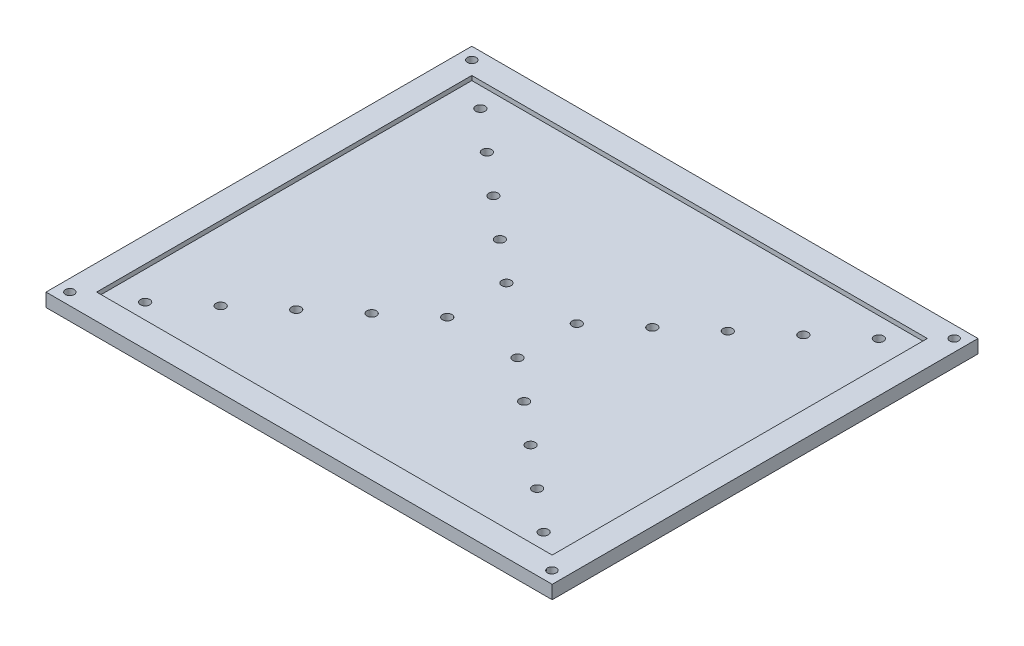
SolidWorks part; units mm, degrees
ref_plane "Front Plane" through (0, 0, 0) normal (0, 0, 1) x (1, 0, 0)
ref_plane "Top Plane" through (0, 0, 0) normal (0, 1, 0) x (1, 0, 0)
ref_plane "Right Plane" through (0, 0, 0) normal (1, 0, 0) x (0, 0, -1)
sketch "Sketch1" plane through (0, 0, 0) normal (0, 1, 0) x (1, 0, 0)
  line L1 (-94.45, 79.45) -> (94.45, 79.45)
  line L2 (-94.45, 79.45) -> (-94.45, -79.45)
  line L3 (-94.45, -79.45) -> (94.45, -79.45)
  line L4 (94.45, 79.45) -> (94.45, -79.45)
  point P4 (0, 79.45)
  point P6 (-94.45, 0)
  dimension "D1" = 158.9
  dimension "D2" = 188.9
extrude "Boss-Extrude1" add sketch "Sketch1" along normal blind 5
sketch "Sketch2" plane through (0, 5, 0) normal (0, 1, 0) x (1, 0, 0)
  line L0 (-94.45, 79.45) -> (-94.45, -79.45) construction
  line L1 (-85, 70) -> (85, 70)
  line L2 (-85, 70) -> (-85, -70)
  line L3 (-85, -70) -> (85, -70)
  line L4 (85, 70) -> (85, -70)
  line L5 (94.45, 79.45) -> (-94.45, 79.45) construction
  point P8 (-85, 0)
  point P10 (0, 70)
  dimension "D1" = 9.45
  dimension "D2" = 9.45
extrude "Cut-Extrude1" cut sketch "Sketch2" against normal blind 1.66
sketch "Sketch3" plane through (0, 5, 0) normal (0, 1, 0) x (1, 0, 0)
  line L0 (-94.45, 79.45) -> (-94.45, -79.45) construction
  line L1 (94.45, 79.45) -> (-94.45, 79.45) construction
  circle A0 centre (-90, 75) radius 1.65
  dimension "D1" = 3.3
  dimension "D2" = 4.45
  dimension "D3" = 4.45
extrude "Cut-Extrude2" cut sketch "Sketch3" against normal blind 5 contours A0
sketch "Sketch6" plane through (0, 5, 0) normal (0, 1, 0) x (1, 0, 0)
  line L0 (-94.45, -79.45) -> (94.45, -79.45) construction
  line L1 (-94.45, 79.45) -> (-94.45, -79.45) construction
  line L2 (94.45, -79.45) -> (94.45, 79.45) construction
  line L3 (94.45, 79.45) -> (-94.45, 79.45) construction
  circle A0 centre (-90, -75) radius 1.65
  circle A1 centre (89.9, -75) radius 1.65
  circle A2 centre (90, 75) radius 1.65
  dimension "D1" = 3.3
  dimension "D6" = 4.45
  dimension "D7" = 4.45
  dimension "D2" = 4.45
  dimension "D3" = 4.45
  dimension "D4" = 4.55
  dimension "D5" = 4.45
extrude "Cut-Extrude4" cut sketch "Sketch6" against normal blind 10
sketch "Sketch7" plane through (0, 3.34, 0) normal (0, 1, 0) x (1, 0, 0)
  line L0 (-2.75, 0) -> (2.75, 0) construction
  line L2 (-94.45, 79.45) -> (0, 0) construction
  line L4 (0, -2.75) -> (0, 2.75) construction
  circle A0 centre (-74.3523, 62.5441) radius 1.75
  circle A1 centre (74.3523, -62.5441) radius 1.75
  circle A2 centre (-59.0471, 49.6696) radius 1.75
  circle A3 centre (-43.742, 36.7951) radius 1.75
  circle A4 centre (-28.4368, 23.9207) radius 1.75
  circle A5 centre (-13.1317, 11.0462) radius 1.75
  circle A6 centre (13.1317, 11.0462) radius 1.75
  circle A7 centre (28.4368, 23.9207) radius 1.75
  circle A8 centre (43.742, 36.7951) radius 1.75
  circle A9 centre (59.0471, 49.6696) radius 1.75
  circle A10 centre (74.3523, 62.5441) radius 1.75
  circle A11 centre (59.0471, -49.6696) radius 1.75
  circle A12 centre (43.742, -36.7951) radius 1.75
  circle A13 centre (28.4368, -23.9207) radius 1.75
  circle A14 centre (13.1317, -11.0462) radius 1.75
  circle A15 centre (-13.1317, -11.0462) radius 1.75
  circle A16 centre (-28.4368, -23.9207) radius 1.75
  circle A17 centre (-43.742, -36.7951) radius 1.75
  circle A18 centre (-59.0471, -49.6696) radius 1.75
  circle A19 centre (-74.3523, -62.5441) radius 1.75
  circle A20 centre (-90, 75) radius 1.65 construction
  point P4 (-73.7265, 62.0177)
  point P18 (0, 0)
  point P19 (-13.0681, 10.9927)
  point P20 (-26.5997, 22.3753)
  point P21 (-44.2496, 37.2222)
  point P22 (-58.3449, 49.0789)
  dimension "D1" = 3.5
  dimension "D2" = 20
  dimension "D3" = 20
  dimension "D4" = 20
  dimension "D5" = 20
  dimension "D6" = 20
extrude "Cut-Extrude5" cut sketch "Sketch7" against normal blind 10
